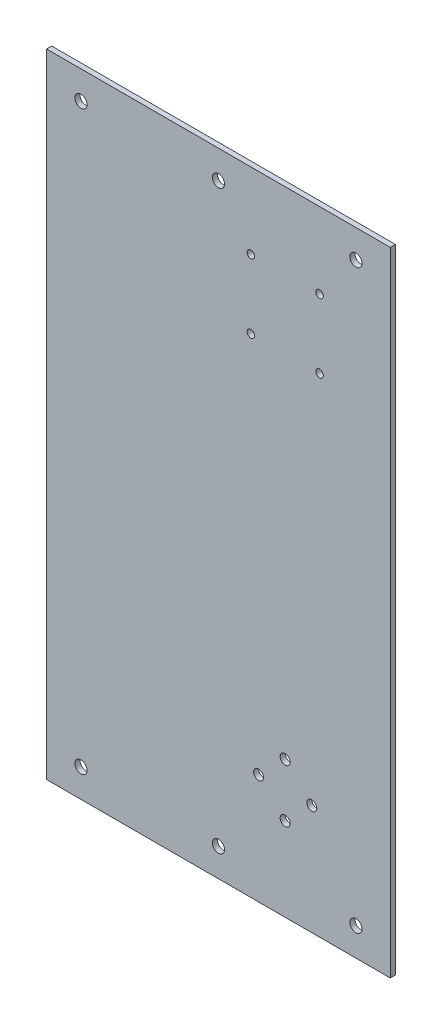
SolidWorks part; units mm, degrees
material "5052-H32"
ref_plane "Front Plane" through (0, 0, 0) normal (0, 0, 1) x (1, 0, 0)
ref_plane "Top Plane" through (0, 0, 0) normal (0, 1, 0) x (1, 0, 0)
ref_plane "Right Plane" through (0, 0, 0) normal (1, 0, 0) x (0, 0, -1)
sketch "Sketch1" plane through (0, 0, 0) normal (0, 0, 1) x (1, 0, 0)
  line L0 (55, 0) -> (-55, 0) construction
  line L1 (-77.5, 142.695) -> (77.5, 142.695)
  line L2 (-77.5, 142.695) -> (-77.5, -142.695)
  line L3 (-77.5, -142.695) -> (77.5, -142.695)
  line L4 (77.5, 142.695) -> (77.5, -142.695)
  line L5 (-77.5, 142.695) -> (77.5, -142.695) construction
  line L6 (-77.5, -142.695) -> (77.5, 142.695) construction
  point P0 (0, 0)
  point P5 (-62, 129.995)
  point P7 (0, 129.995)
  point P8 (62, 129.995)
  point P13 (62, -129.995)
  point P14 (0, -129.995)
  point P15 (-62, -129.995)
  dimension "D1" = 155
  dimension "D2" = 285.39
  dimension "D3" = 15.5
  dimension "D4" = 15.5
  dimension "D5" = 12.7
extrude "Boss-Extrude1" add sketch "Sketch1" along normal blind 2.305
hole_wizard "M5 Clearance Hole1" positions "Sketch2" profile "Sketch3" hole size "M5" standard "ANSI Metric" end condition through all
sketch "Sketch2" plane through (0, 0, 2.305) normal (0, 0, 1) x (1, 0, 0)
  point P0 (-62, 129.995)
  point P3 (0, 129.995)
  point P9 (-62, -129.995)
  point P12 (0, -129.995)
  point P15 (62, -129.995)
sketch "Sketch3" plane through (-62, 129.995, 2.305) normal (1, 0, 0) x (0, -1, 0)
  line L0 (0, 0) -> (0, 2.305)
  line L1 (0, 2.305) -> (2.75, 2.305)
  line L2 (2.75, 2.305) -> (2.75, 0)
  line L5 (2.75, 0) -> (0, 0)
  line L11 (0, -6.35) -> (0, 107.95) construction
  dimension "Thru Hole Dia." = 5.5
  dimension "Thru Hole Depth" = 2.305
sketch "Sketch4" plane through (0, 0, 2.305) normal (0, 0, 1) x (1, 0, 0)
  line L0 (18.1, -93) -> (42.1, -93) construction
  line L1 (30.1, -81) -> (30.1, -105) construction
  line L2 (-77.5, -142.695) -> (77.5, -142.695) construction
  line L4 (77.5, -142.695) -> (77.5, 142.695) construction
  line L5 (30.1, -93) -> (30.1, 93) construction
  line L6 (77.5, 142.695) -> (-77.5, 142.695) construction
  line L7 (14.6, 77.5) -> (45.6, 77.5) construction
  line L8 (14.6, 77.5) -> (14.6, 108.5) construction
  line L9 (14.6, 108.5) -> (45.6, 108.5) construction
  line L10 (45.6, 77.5) -> (45.6, 108.5) construction
  line L11 (14.6, 77.5) -> (45.6, 108.5) construction
  line L12 (14.6, 108.5) -> (45.6, 77.5) construction
  circle A0 centre (30.1, -93) radius 16 construction
  circle A1 centre (30.1, -93) radius 12 construction
  circle A2 centre (30.1, -81) radius 2.25
  circle A3 centre (42.1, -93) radius 2.25
  circle A4 centre (30.1, -105) radius 2.25
  circle A5 centre (18.1, -93) radius 2.25
  circle A6 centre (30.1, 93) radius 3.25 construction
  circle A7 centre (45.6, 108.5) radius 1.7
  circle A8 centre (14.6, 77.5) radius 1.7
  circle A9 centre (45.6, 77.5) radius 1.7
  circle A10 centre (14.6, 108.5) radius 1.7
  dimension "D1" = 32
  dimension "D2" = 24
  dimension "D3" = 4.5
  dimension "D6" = 6.5
  dimension "D9" = 3.4
  dimension "D4" = 49.695
  dimension "D5" = 47.4
  dimension "D7" = 49.695
  dimension "D8" = 31
extrude "Cut-Extrude1" cut sketch "Sketch4" against normal through all
mirror "Mirror1" about plane through (0, 0, 0) normal (0, 1, 0) of "M5 Clearance Hole1"
equation "\"D2@Sketch4\"=(32+16)/2"
equation "\"D7@Sketch4\"=\"D4@Sketch4\""
